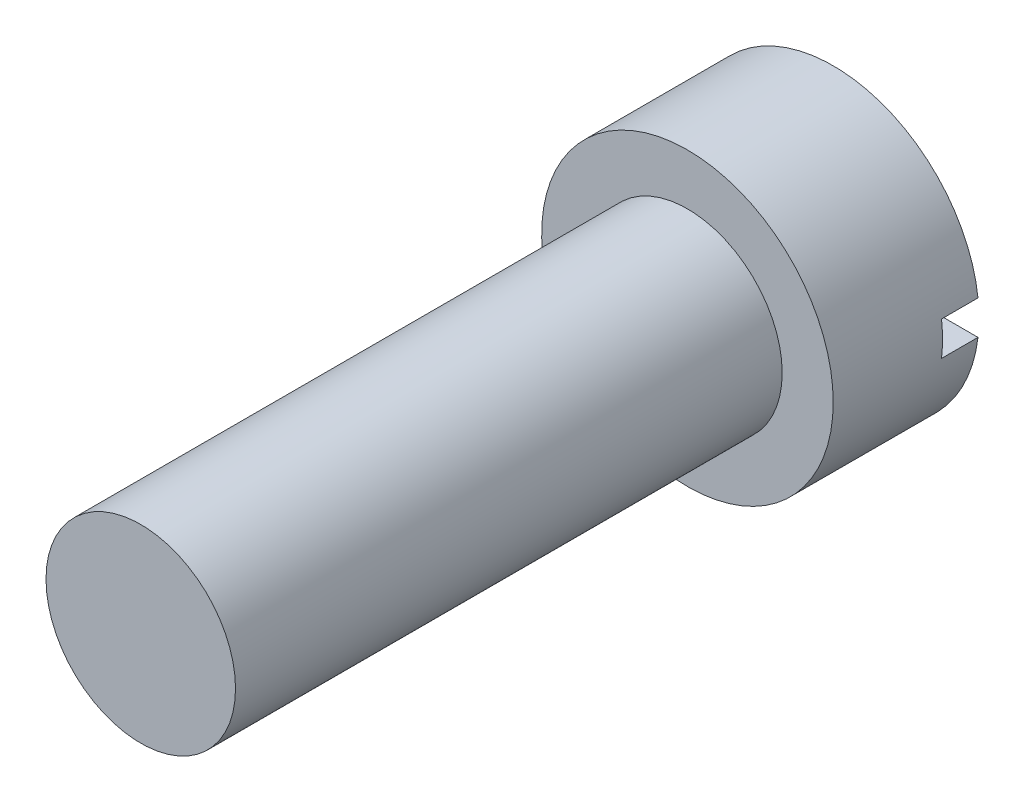
SolidWorks part; units mm, degrees
material "1.5714 (16NiCr4)"
ref_plane "Plan de face" through (0, 0, 0) normal (0, 0, 1) x (1, 0, 0)
ref_plane "Plan de dessus" through (0, 0, 0) normal (0, 1, 0) x (1, 0, 0)
ref_plane "Plan de droite" through (0, 0, 0) normal (1, 0, 0) x (0, 0, -1)
sketch "Esquisse1" plane through (0, 0, 0) normal (0, 0, 1) x (1, 0, 0)
  circle A0 centre (0, 0) radius 2
  dimension "D1" = 4
extrude "Boss.-Extru.1" add sketch "Esquisse1" along normal blind 2
sketch "Esquisse2" plane through (0, 0, 2) normal (0, 0, 1) x (1, 0, 0)
  circle A0 centre (0, 0) radius 1.3
  dimension "D1" = 2.6
extrude "Boss.-Extru.2" add sketch "Esquisse2" along normal blind 7.5
sketch "Esquisse3" plane through (0, 0, 0) normal (0, 0, -1) x (-1, 0, 0)
  line L1 (-2.5277, -0.2343) -> (2.5277, -0.2343)
  line L2 (-2.5277, -0.2343) -> (-2.5277, 0.2343)
  line L3 (-2.5277, 0.2343) -> (2.5277, 0.2343)
  line L4 (2.5277, -0.2343) -> (2.5277, 0.2343)
  line L5 (-2.5277, -0.2343) -> (2.5277, 0.2343) construction
  line L6 (-2.5277, 0.2343) -> (2.5277, -0.2343) construction
  point P0 (0, 0)
extrude "Enlèv. mat.-Extru.1" cut sketch "Esquisse3" against normal blind 0.5
